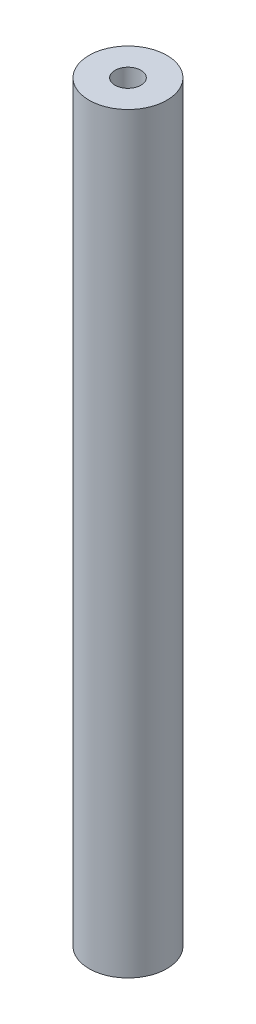
SolidWorks part; units mm, degrees
ref_plane "Front Plane" through (0, 0, 0) normal (0, 0, 1) x (1, 0, 0)
ref_plane "Top Plane" through (0, 0, 0) normal (0, 1, 0) x (1, 0, 0)
ref_plane "Right Plane" through (0, 0, 0) normal (1, 0, 0) x (0, 0, -1)
sketch "Sketch1" plane through (0, 0, 0) normal (0, 1, 0) x (1, 0, 0)
  circle A0 centre (0, 0) radius 0.5
  circle A1 centre (0, 0) radius 1.5
  dimension "D1" = 1
  dimension "D2" = 3
extrude "Boss-Extrude1" add sketch "Sketch1" along normal blind 29
